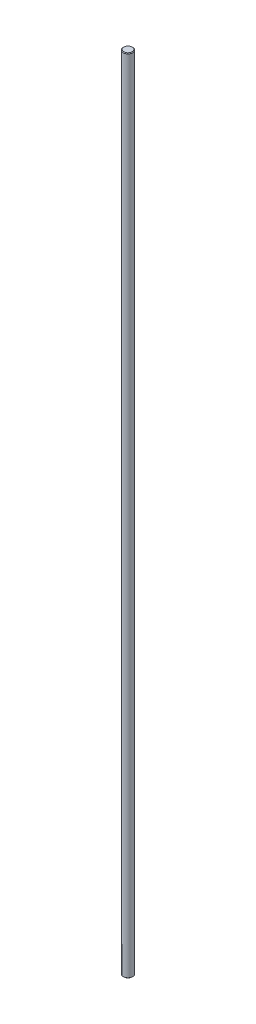
SolidWorks part; units mm, degrees
material "Acero inoxidable al cromo"
ref_plane "Alzado" through (0, 0, 0) normal (0, 0, 1) x (1, 0, 0)
ref_plane "Planta" through (0, 0, 0) normal (0, 1, 0) x (1, 0, 0)
ref_plane "Vista lateral" through (0, 0, 0) normal (1, 0, 0) x (0, 0, -1)
sketch "Croquis1" plane through (0, 0, 0) normal (0, 1, 0) x (1, 0, 0)
  circle A0 centre (0, 0) radius 4
  circle A1 centre (0, 0) radius 3 construction
  dimension "D1" = 8
  dimension "D2" = 6
extrude "Saliente-Extruir1" add sketch "Croquis1" along normal blind 675
chamfer "Chaflán1" distance 0.5 angle 45 2 edges at (0, 0, 4) (0, 675, 4)
